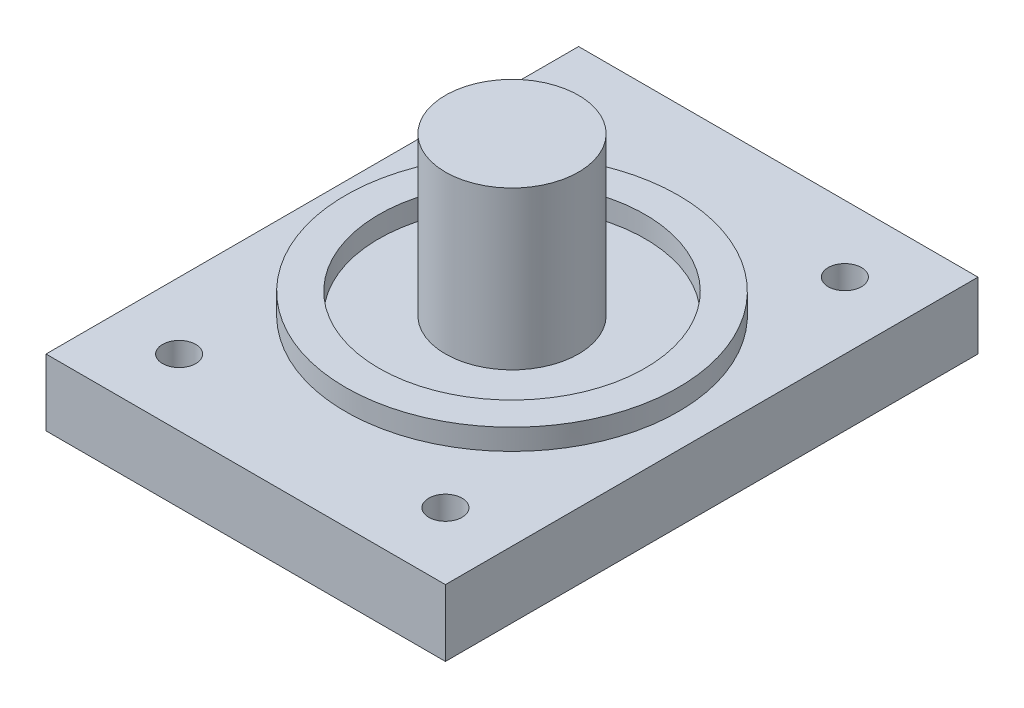
SolidWorks part; units mm, degrees
ref_plane "Front Plane" through (0, 0, 0) normal (0, 0, 1) x (1, 0, 0)
ref_plane "Top Plane" through (0, 0, 0) normal (0, 1, 0) x (1, 0, 0)
ref_plane "Right Plane" through (0, 0, 0) normal (1, 0, 0) x (0, 0, -1)
sketch "Sketch1" plane through (0, 0, 0) normal (0, 1, 0) x (1, 0, 0)
  line L1 (0, 0) -> (19.05, 0)
  line L2 (0, 0) -> (0, 25.4)
  line L3 (0, 25.4) -> (19.05, 25.4)
  line L4 (19.05, 0) -> (19.05, 25.4)
  dimension "D1" = 19.05
  dimension "D2" = 25.4
extrude "Boss-Extrude1" add sketch "Sketch1" along normal blind 3.175
sketch "Sketch2" plane through (0, 3.175, 0) normal (0, 1, 0) x (1, 0, 0)
  line L0 (0, 25.4) -> (0, 0) construction
  line L1 (19.05, 0) -> (19.05, 25.4) construction
  line L2 (0, 25.4) -> (0, 0) construction
  line L3 (19.05, 0) -> (19.05, 25.4) construction
  line L4 (0, 12.7) -> (19.05, 12.7) construction
  circle A0 centre (9.525, 12.7) radius 3.175
  dimension "D1" = 6.35
extrude "Boss-Extrude2" add sketch "Sketch2" along normal blind 7.5125
sketch "Sketch3" plane through (0, 3.175, 0) normal (0, 1, 0) x (1, 0, 0)
  line L0 (19.05, 25.4) -> (0, 25.4) construction
  line L1 (19.05, 25.4) -> (0, 25.4) construction
  line L2 (3.175, 22.225) -> (15.875, 22.225) construction
  line L3 (3.175, 3.175) -> (15.875, 3.175) construction
  line L5 (0, 0) -> (19.05, 0) construction
  circle A0 centre (3.175, 22.225) radius 0.7938
  circle A1 centre (15.875, 22.225) radius 0.7937
  circle A2 centre (15.875, 3.175) radius 0.7937
  circle A3 centre (3.175, 3.175) radius 0.7938
  point P6 (9.525, 25.4)
  point P7 (9.525, 22.225)
  point P8 (9.525, 3.175)
  dimension "D4" = 1.5875
  dimension "D1" = 3.175
  dimension "D2" = 3.175
  dimension "D3" = 12.7
extrude "Cut-Extrude1" cut sketch "Sketch3" against normal up to surface (3.175 mm away) up to face at (9.525, 0, -12.7)
sketch "Sketch4" plane through (0, 3.175, 0) normal (0, 1, 0) x (1, 0, 0)
  circle A0 centre (9.525, 12.7) radius 7.9375
  circle A1 centre (9.525, 12.7) radius 6.35
  dimension "D1" = 15.875
  dimension "D2" = 12.7
extrude "Boss-Extrude3" add sketch "Sketch4" along normal blind 1
